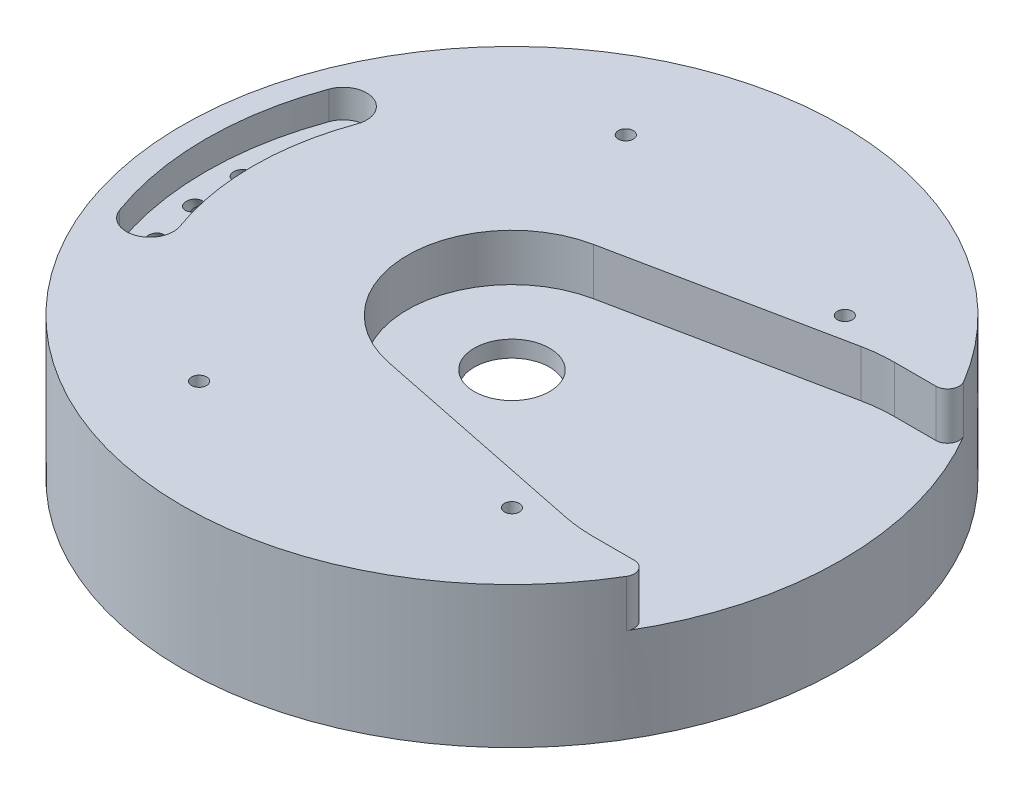
SolidWorks part; units mm, degrees
material "1023 Carbon Steel Sheet (SS)"
ref_plane "Front Plane" through (0, 0, 0) normal (0, 0, 1) x (1, 0, 0)
ref_plane "Top Plane" through (0, 0, 0) normal (0, 1, 0) x (1, 0, 0)
ref_plane "Right Plane" through (0, 0, 0) normal (1, 0, 0) x (0, 0, -1)
ref_axis "Axis1" through (0, 17.78, 0) along (0, -1, 0)
sketch "Sketch9" plane through (0, 0, 0) normal (0, 0, 1) x (1, 0, 0)
  line L0 (-10.16, 10.16) -> (-10.16, 27.305)
  line L1 (-10.16, 27.305) -> (-88.9, 27.305)
  line L2 (-88.9, 27.305) -> (-88.9, -10.795)
  line L3 (-88.9, -10.795) -> (-80.645, -10.795)
  line L4 (-80.645, -10.795) -> (-80.645, 10.795)
  line L5 (-80.645, 10.795) -> (-69.85, 10.795)
  line L6 (-69.85, 10.795) -> (-69.85, 5.08)
  line L10 (0, 18.1217) -> (0, -20.6688) construction
  line L11 (-69.85, 5.08) -> (-58.42, 5.08)
  line L12 (-58.42, 5.08) -> (-58.42, 6.35)
  line L13 (-58.42, 6.35) -> (-45.72, 6.35)
  line L14 (-45.72, 6.35) -> (-45.72, 7.62)
  line L15 (-45.72, 7.62) -> (-33.02, 7.62)
  line L16 (-33.02, 7.62) -> (-33.02, 10.16)
  line L17 (-33.02, 10.16) -> (-10.16, 10.16)
  line L18 (-80.645, 9.525) -> (0, 9.525) construction
  line L19 (-80.645, 0) -> (0, 0) construction
  dimension "D1" = 20.32
  dimension "D2" = 177.8
  dimension "D5" = 38.1
  dimension "D6" = 161.29
  dimension "D3" = 9.525
  dimension "D4" = 5.08
  dimension "D8" = 58.42
  dimension "D9" = 6.35
  dimension "D10" = 45.72
  dimension "D11" = 7.62
  dimension "D12" = 33.02
  dimension "D13" = 10.16
  dimension "D7" = 69.85
  dimension "D15" = 17.78
  dimension "D14" = 1.27
revolve "Revolve1" add sketch "Sketch9" angle 360 about L10
sketch "Sketch1" plane through (0, 27.305, 0) normal (0, 1, 0) x (1, 0, 0)
  line L0 (-76.9897, -44.45) -> (-50.8, -44.45)
  line L1 (-50.8, -44.45) -> (-50.8, 44.45)
  line L2 (-50.8, 44.45) -> (-76.9897, 44.45)
  line L3 (-5, 24.4949) -> (55, 36.7423) construction
  line L4 (-5, -24.4949) -> (55, -36.7423) construction
  line L5 (-5.635, -27.6057) -> (54.365, -39.8532)
  line L6 (-5.635, 27.6057) -> (54.365, 39.8532)
  line L7 (62.5, 40.675) -> (79.0491, 40.675)
  line L8 (62.5, -40.675) -> (79.0491, -40.675)
  circle A0 centre (0, 0) radius 88.9
  circle A3 centre (0, 0) radius 76.2 construction
  circle A4 centre (0, 0) radius 25 construction
  circle A5 centre (62.5, 0) radius 37.5 construction
  circle A6 centre (0, 0) radius 28.175
  circle A7 centre (62.5, 0) radius 40.675
  point P8 (-50.8, 0)
  dimension "D1" = 177.8
  dimension "D2" = 50
  dimension "D6" = 75
  dimension "D4" = 152.4
  dimension "D3" = 88.9
  dimension "D5" = 50.8
  dimension "D7" = 3.175
  dimension "D8" = 3.175
  dimension "D9" = 3.175
extrude "Gear Slot" cut sketch "Sketch1" against normal blind 12.7 contours A7 A6 | A0 A7 A6 | A7 L6 A6 | A7 A6 L5 | A6 A7 | A7 A0 L7 | A7 L8 A0
ref_plane "Plane2" through (-76.2, 0, 0) normal (1, 0, 0) x (0, 0, -1)
sketch "Sketch10" plane through (0, 27.305, 0) normal (0, 1, 0) x (1, 0, 0)
  line L0 (0, 0) -> (-71.6046, 26.0619) construction
  line L1 (0, 0) -> (-71.6046, -26.0619) construction
  arc A0 (-65.6375, -23.8901) -> (-65.6375, 23.8901) centre (0, 0) cw
  arc A1 (-77.5716, -28.2338) -> (-77.5716, 28.2338) centre (0, 0) cw
  arc A2 (-71.6046, -26.0619) -> (-71.6046, 26.0619) centre (0, 0) cw construction
  arc A3 (-77.5716, 28.2338) -> (-65.6375, 23.8901) centre (-71.6046, 26.0619) cw
  arc A4 (-65.6375, -23.8901) -> (-77.5716, -28.2338) centre (-71.6046, -26.0619) cw
  point P9 (-82.55, 0)
  dimension "D1" = 76.2
  dimension "D2" = 12.7
  dimension "D3" = 40
sketch "Sketch5" plane through (-76.2, 0, 0) normal (1, 0, 0) x (0, 0, -1)
  line L0 (-7.555, 3.092) -> (-10.0638, 15.9985)
  line L1 (-10.0638, 15.9985) -> (-12.2907, 20.5643)
  line L2 (-12.2907, 20.5643) -> (-8.638, 22.3459)
  line L3 (-8.638, 22.3459) -> (-6.4111, 17.78)
  line L4 (-6.4111, 17.78) -> (2.2148, 7.8571)
  line L5 (2.2148, 7.8571) -> (-7.555, 3.092)
  line L6 (-2.6701, 5.4745) -> (-10.4644, 21.4551)
  line L7 (-10.0638, 15.9985) -> (-6.4111, 17.78) construction
  line L8 (-2.6701, 5.4745) -> (-2.6701, 23.0928) construction
  line L9 (-2.6701, 5.4745) -> (0, 0) construction
  dimension "D2" = 15
  dimension "D3" = 4.064
  dimension "D5" = 12.7
  dimension "D6" = 5.08
  dimension "D1" = 26
  dimension "D4" = 17.78
revolve "Orifice" cut sketch "Sketch5" angle 360 about L6
pattern_circular "CirPattern1" count 2 over 10 about axis through (0, 17.78, 0) along (0, -1, 0) of "Orifice"
sketch "Stock Sketch" plane through (0, 27.305, 0) normal (0, 1, 0) x (1, 0, 0)
  circle A0 centre (0, 0) radius 88.9
  dimension "D1" = 177.8
extrude "Gas Manifold" cut sketch "Sketch10" against normal blind 7.62
fillet "Fillet1" radius 3.175 2 edges at (79.0491, 20.955, -40.675) (79.0491, 20.955, 40.675)
ref_plane "Plane3" through (0, 0, 0) normal (0, -1, 0) x (-1, 0, 0)
hole_wizard "Tap Drill for #10-32 Tap1" positions "3DSketch1" profile "Sketch12" hole size "#10-32" standard "ANSI Inch"
sketch3d "3DSketch1"
  line L5 (0, 0, 0) -> (0, 27.305, 0) construction
  line L7 (0, 27.305, 0) -> (44.9013, 27.305, -44.9013) construction
  line L10 (0, 27.305, 0) -> (44.9013, 27.305, 0) construction
  line L14 (-26.8363, 27.305, -57.5505) -> (0, 27.305, 0) construction
  line L15 (0, 27.305, 0) -> (-26.8363, 27.305, 57.5505) construction
  line L16 (0, 27.305, 0) -> (44.9013, 27.305, 44.9013) construction
  line L20 (0, 27.305, 0) -> (-48.2117, 27.305, 0) construction
  point P0 (44.9013, 27.305, -44.9013)
  point P2 (-26.8363, 27.305, -57.5505)
  point P4 (-26.8363, 27.305, 57.5505)
  point P6 (44.9013, 27.305, 44.9013)
  dimension "D1" = 63.5
  dimension "D2" = 45
  dimension "D3" = 65
sketch "Sketch12" plane through (44.9013, 27.305, -44.9013) normal (1, 0, 0) x (0, 0, 1)
  line L0 (0, 0) -> (0, 19.05)
  line L1 (0, 19.05) -> (2.0193, 17.8367)
  line L2 (2.0193, 17.8367) -> (2.0193, 0)
  line L5 (2.0193, 0) -> (0, 0)
  line L10 (0, 19.05) -> (-2.0193, 17.8367) construction
  line L11 (0, -6.35) -> (0, 107.95) construction
  dimension "Hole Dia." = 4.0386
  dimension "Hole Depth" = 19.05
  dimension "Drill Angle" = 118
equation "\"D3@Sketch5\"=\"nozzle diameter@[TP] [Turb] Turbine.Assembly\""
equation "\"D6@Sketch9\"=2*(\"rotor tip@[TP] [Turb] Turbine.Assembly\"+\"rotor clearance@[TP] [Turb] Turbine.Assembly\")"
